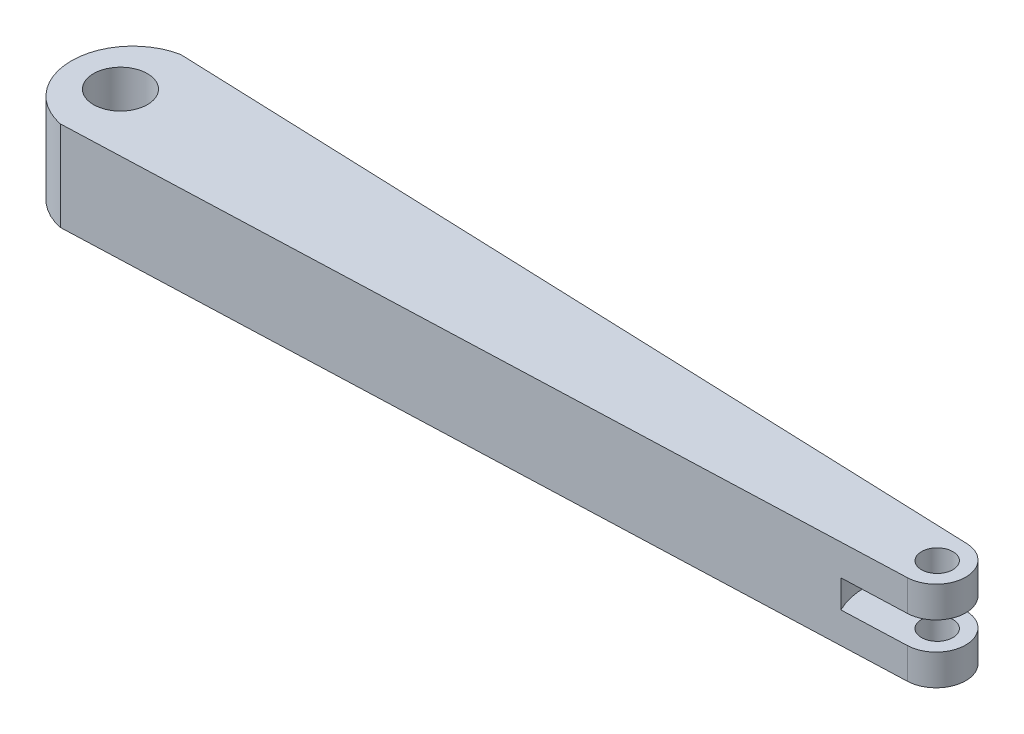
SolidWorks part; units mm, degrees
ref_plane "Front Plane" through (0, 0, 0) normal (0, 0, 1) x (1, 0, 0)
ref_plane "Top Plane" through (0, 0, 0) normal (0, 1, 0) x (1, 0, 0)
ref_plane "Right Plane" through (0, 0, 0) normal (1, 0, 0) x (0, 0, -1)
sketch "Sketch1" plane through (0, 0, 0) normal (0, 1, 0) x (1, 0, 0)
  line L0 (-24.0492, 0) -> (66.9508, 0) construction
  line L1 (-24.0492, 6.7) -> (66.9508, 3.3)
  line L2 (-24.0492, -6.7) -> (66.9508, -3.3)
  circle A0 centre (66.9508, 0) radius 1.75
  circle A1 centre (-24.0492, 0) radius 3
  arc A2 (66.9508, 3.3) -> (66.9508, -3.3) centre (66.8275, 0) cw
  arc A3 (-24.0492, 6.7) -> (-24.0492, -6.7) centre (-22.6836, 0) ccw
  dimension "D1" = 6
  dimension "D2" = 3.5
  dimension "D3" = 91
  dimension "D4" = 6.7
  dimension "D5" = 3.3
extrude "Boss-Extrude1" add sketch "Sketch1" along normal blind 10
ref_plane "Plane1" through (66.9508, 0, 0) normal (1, 0, 0) x (0, 0, -1)
sketch "Sketch2" plane through (66.9508, 0, 0) normal (1, 0, 0) x (0, 0, -1)
  line L0 (0, 6.55) -> (8, 6.55)
  line L1 (0, 10) -> (0, 0) construction
  line L2 (8, 6.55) -> (8, 3.45)
  line L3 (8, 3.45) -> (0, 3.45)
  line L4 (0, 3.45) -> (0, 6.55)
  line L5 (3.3, 10) -> (-3.3, 10) construction
  point P5 (0, 5)
  dimension "D1" = 3.1
  dimension "D2" = 5
  dimension "D3" = 8
revolve "Cut-Revolve1" cut sketch "Sketch2" angle 360 about L4
